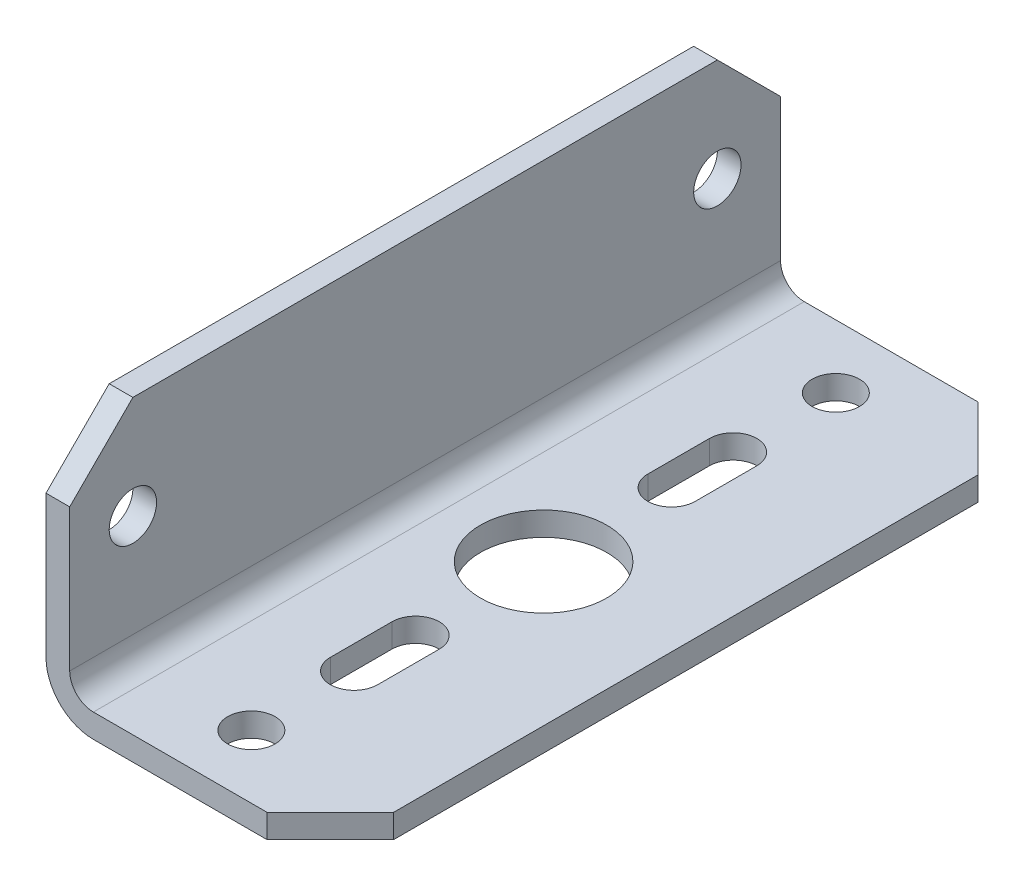
SolidWorks part; units mm, degrees
material "3.3535 (EN-AW 5754)"
ref_plane "Front" through (0, 0, 0) normal (0, 0, 1) x (1, 0, 0)
ref_plane "Top" through (0, 0, 0) normal (0, 1, 0) x (1, 0, 0)
ref_plane "Right" through (0, 0, 0) normal (1, 0, 0) x (0, 0, -1)
sketch "Эскиз1" plane through (0, 0, 0) normal (0, 0, 1) x (1, 0, 0)
  line L0 (0, 0) -> (0, 16)
  line L1 (0, 16) -> (1.5, 16)
  line L2 (1.5, 16) -> (1.5, 1.5)
  line L3 (0, 0) -> (18, 0)
  line L4 (18, 0) -> (18, 1.5)
  line L5 (18, 1.5) -> (1.5, 1.5)
  dimension "D1" = 16
  dimension "D2" = 18
  dimension "D3" = 1.5
  dimension "D4" = 1.5
extrude "Бобышка-Вытянуть1" add sketch "Эскиз1" along normal mid plane 45
sketch "Эскиз2" plane through (0, 1.5, 0) normal (0, 1, 0) x (1, 0, 0)
  line L0 (18, 0) -> (9, 0) construction
  line L1 (18, -22.5) -> (18, 22.5) construction
  line L2 (9, 0) -> (9, 6.3835) construction
  line L3 (9, 0) -> (-3.2605, 0) construction
  line L4 (7.5, 8.1) -> (7.5, 12)
  line L5 (10.5, -12) -> (10.5, -8.1)
  line L6 (10.5, 12) -> (10.5, 8.1)
  line L7 (7.5, -8.1) -> (7.5, -12)
  circle A0 centre (9, 0) radius 4
  circle A1 centre (9, 18.5) radius 1.5
  arc A2 (7.5, 8.1) -> (10.5, 8.1) centre (9, 8.1) ccw
  arc A3 (10.5, 12) -> (7.5, 12) centre (9, 12) ccw
  arc A4 (10.5, -12) -> (7.5, -12) centre (9, -12) cw
  arc A5 (7.5, -8.1) -> (10.5, -8.1) centre (9, -8.1) cw
  circle A6 centre (9, -18.5) radius 1.5
  dimension "D1" = 9
  dimension "D2" = 8
  dimension "D3" = 18.5
  dimension "D4" = 3
  dimension "D5" = 16.2
  dimension "D6" = 24
  dimension "D7" = 37
extrude "Вырез-Вытянуть1" cut sketch "Эскиз2" against normal blind 45.2
chamfer "Фаска1" distance 4 angle 45 4 edges at (18, 0.75, -22.5) (18, 0.75, 22.5) (0.75, 16, 22.5) (0.75, 16, -22.5)
fillet "Скругление1" radius 1.5 1 edges at (1.5, 1.5, 0)
fillet "Скругление2" radius 3 1 edges at (0, 0, 0)
sketch "Эскиз4" plane through (0, 0, 0) normal (-1, 0, 0) x (0, 0, 1)
  line L0 (0, 0) -> (0, 9.5)
  line L2 (0, 9.5) -> (28.2317, 9.5) construction
  circle A0 centre (0, 9.5) radius 18.5 construction
  circle A1 centre (-18.5, 9.5) radius 1.5
  circle A2 centre (18.5, 9.5) radius 1.5
  dimension "D1" = 9.5
extrude "Вырез-Вытянуть2" cut sketch "Эскиз4" against normal through all contours A1 | A2
